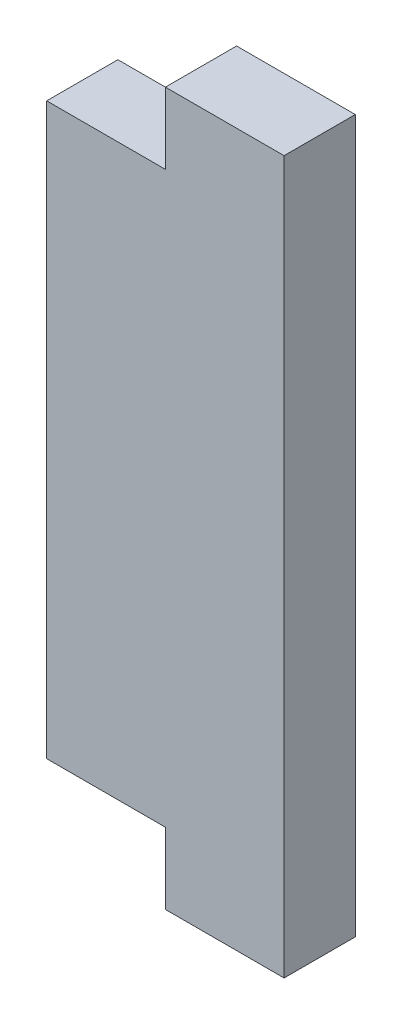
SolidWorks part; units mm, degrees
ref_plane "Front Plane" through (0, 0, 0) normal (0, 0, 1) x (1, 0, 0)
ref_plane "Top Plane" through (0, 0, 0) normal (0, 1, 0) x (1, 0, 0)
ref_plane "Right Plane" through (0, 0, 0) normal (1, 0, 0) x (0, 0, -1)
sketch "Sketch1" plane through (0, 0, 0) normal (0, 0, 1) x (1, 0, 0)
  line L1 (-10, 60) -> (0, 60)
  line L2 (-20, 54) -> (-20, 6)
  line L3 (-10, 0) -> (0, 0)
  line L4 (0, 60) -> (0, 0)
  line L7 (-20, 54) -> (-10, 54)
  line L8 (-10, 60) -> (-10, 54)
  line L11 (-20, 6) -> (-10, 6)
  line L12 (-10, 0) -> (-10, 6)
  dimension "D1" = 20
  dimension "D2" = 60
  dimension "D3" = 10
  dimension "D4" = 6
  dimension "D5" = 10
  dimension "D6" = 6
extrude "Boss-Extrude1" add sketch "Sketch1" along normal blind 6
